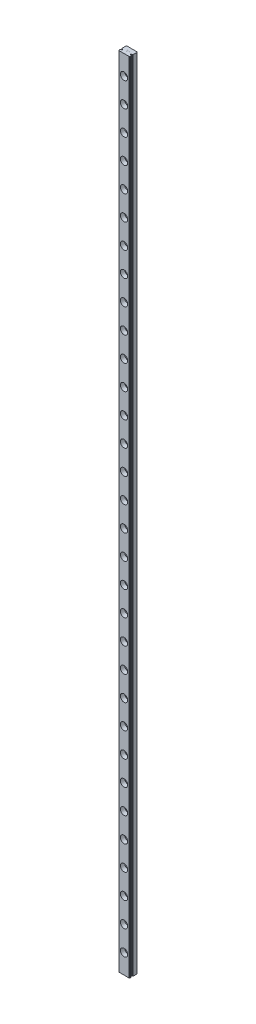
SolidWorks part; units mm, degrees
material "acero"
ref_plane "Alzado" through (0, 0, 0) normal (0, 0, 1) x (1, 0, 0)
ref_plane "Planta" through (0, 0, 0) normal (0, 1, 0) x (1, 0, 0)
ref_plane "Vista lateral" through (0, 0, 0) normal (1, 0, 0) x (0, 0, -1)
ref_plane "Plano1" through (0, 0, 0) normal (0, -1, 0) x (1, 0, 0)
sketch "Croquis1" plane through (0, 0, 0) normal (0, -1, 0) x (1, 0, 0)
  line L0 (4.5, 0) -> (4.5, 6.0117)
  line L1 (4.5, 6.0117) -> (4.1, 6.5)
  line L2 (4.1, 6.5) -> (-4.1, 6.5)
  line L3 (-4.1, 6.5) -> (-4.5, 6.0117)
  line L4 (-4.5, 6.0117) -> (-4.5, 0)
  line L5 (-4.5, 0) -> (4.5, 0)
extrude "Saliente-Extruir1" add sketch "Croquis1" against normal blind 652
sketch "Croquis2" plane through (0, 652, 0) normal (0, 1, 0) x (-1, 0, 0)
  line L0 (-4.5, 4.8802) -> (-4.5, 4.0315)
  line L1 (-4.5, 4.0315) -> (-3.8193, 4.0315)
  line L2 (-3.8193, 4.8802) -> (-4.5, 4.8802)
  arc A1 (-3.8193, 4.0315) -> (-3.8193, 4.8802) centre (-3.6695, 4.4558) ccw
  dimension "D4" = 0.9
  dimension "D2" = 0.8487
extrude "Cortar-Extruir1" cut sketch "Croquis2" against normal through all
sketch "Croquis3" plane through (0, 652, 0) normal (0, 1, 0) x (-1, 0, 0)
  line L0 (-4.0265, 4.0315) -> (-4.5, 4.0315)
  line L1 (-4.5, 4.0315) -> (-4.5, 3.5836)
  arc A0 (-4.5, 3.5836) -> (-4.0265, 4.0315) centre (-4.8765, 4.4558) ccw
extrude "Cortar-Extruir2" cut sketch "Croquis3" against normal through all
sketch "Croquis4" plane through (0, 652, 0) normal (0, 1, 0) x (-1, 0, 0)
  line L0 (-4.5, 5.3281) -> (-4.5, 4.8802)
  line L1 (-4.5, 4.8802) -> (-4.0265, 4.8802)
  arc A0 (-4.0265, 4.8802) -> (-4.5, 5.3281) centre (-4.8765, 4.4558) ccw
extrude "Cortar-Extruir3" cut sketch "Croquis4" against normal through all
sketch "Croquis5" plane through (0, 652, 0) normal (0, 1, 0) x (-1, 0, 0)
  line L0 (4.5, 4.0315) -> (4.5, 4.8802)
  line L1 (4.5, 4.8802) -> (3.8193, 4.8802)
  line L2 (3.8193, 4.0315) -> (4.5, 4.0315)
  arc A1 (3.8193, 4.8802) -> (3.8193, 4.0315) centre (3.6695, 4.4558) ccw
  dimension "D3" = 0.9
  dimension "D2" = 0.8487
extrude "Cortar-Extruir4" cut sketch "Croquis5" against normal through all
sketch "Croquis6" plane through (0, 652, 0) normal (0, 1, 0) x (-1, 0, 0)
  line L0 (4.0265, 4.8802) -> (4.5, 4.8802)
  line L1 (4.5, 4.8802) -> (4.5, 5.3281)
  arc A0 (4.5, 5.3281) -> (4.0265, 4.8802) centre (4.8765, 4.4558) ccw
extrude "Cortar-Extruir5" cut sketch "Croquis6" against normal through all
sketch "Croquis7" plane through (0, 652, 0) normal (0, 1, 0) x (-1, 0, 0)
  line L0 (4.5, 3.5836) -> (4.5, 4.0315)
  line L1 (4.5, 4.0315) -> (4.0265, 4.0315)
  arc A0 (4.0265, 4.0315) -> (4.5, 3.5836) centre (4.8765, 4.4558) ccw
extrude "Cortar-Extruir6" cut sketch "Croquis7" against normal through all
sketch "Croquis8" plane through (0, 652, 0) normal (0, 1, 0) x (-1, 0, 0)
  line L0 (0.8914, 3.4037) -> (0.7147, 3.1682)
  line L1 (0.7147, 3.1682) -> (0.2187, 2.611)
  line L2 (0.2187, 2.611) -> (1.0946, 2.6111)
  line L3 (1.0946, 2.6111) -> (1.0946, 2.696)
  line L4 (1.0946, 2.696) -> (0.3987, 2.696)
  line L5 (0.3987, 2.696) -> (0.7943, 3.1495)
  line L6 (0.7943, 3.1495) -> (0.9743, 3.3891)
  line L7 (0.9743, 3.3891) -> (1.0671, 3.5734)
  line L8 (1.0671, 3.5734) -> (0.9541, 3.8023)
  line L9 (0.9541, 3.8023) -> (0.7877, 3.8851)
  line L10 (0.7877, 3.8851) -> (0.543, 3.8851)
  line L11 (0.543, 3.8851) -> (0.3754, 3.8036)
  line L12 (0.3754, 3.8036) -> (0.295, 3.6384)
  line L13 (0.295, 3.6384) -> (0.295, 3.562)
  line L14 (0.295, 3.562) -> (0.3813, 3.562)
  line L15 (0.3813, 3.562) -> (0.3813, 3.6318)
  line L16 (0.3813, 3.6318) -> (0.4377, 3.7436)
  line L17 (0.4377, 3.7436) -> (0.5496, 3.8001)
  line L18 (0.5496, 3.8001) -> (0.7802, 3.8001)
  line L19 (0.7802, 3.8001) -> (0.893, 3.7438)
  line L20 (0.893, 3.7438) -> (0.9762, 3.576)
  line L21 (0.9762, 3.576) -> (0.8914, 3.4037)
extrude "Cortar-Extruir7" cut sketch "Croquis8" against normal blind 0.0022
sketch "Croquis9" plane through (0, 0, 0) normal (0, -1, 0) x (1, 0, 0)
  line L0 (-0.2146, 3.8851) -> (-0.954, 3.8851)
  line L1 (-0.954, 3.8851) -> (-0.954, 2.6111)
  line L2 (-0.954, 2.6111) -> (-0.2146, 2.6111)
  line L3 (-0.2146, 2.6111) -> (-0.2146, 2.696)
  line L4 (-0.2146, 2.696) -> (-0.869, 2.696)
  line L5 (-0.869, 2.696) -> (-0.869, 3.2056)
  line L6 (-0.869, 3.2056) -> (-0.5124, 3.2056)
  line L7 (-0.5124, 3.2056) -> (-0.5124, 3.2905)
  line L8 (-0.5124, 3.2905) -> (-0.869, 3.2905)
  line L9 (-0.869, 3.2905) -> (-0.869, 3.8001)
  line L10 (-0.869, 3.8001) -> (-0.2146, 3.8001)
  line L11 (-0.2146, 3.8001) -> (-0.2146, 3.8851)
extrude "Cortar-Extruir8" cut sketch "Croquis9" against normal blind 0.0022
sketch "Croquis10" plane through (0, 652, 0) normal (0, 1, 0) x (-1, 0, 0)
  line L0 (-0.2146, 3.8851) -> (-0.954, 3.8851)
  line L1 (-0.954, 3.8851) -> (-0.954, 2.6111)
  line L2 (-0.954, 2.6111) -> (-0.2146, 2.6111)
  line L3 (-0.2146, 2.6111) -> (-0.2146, 2.696)
  line L4 (-0.2146, 2.696) -> (-0.869, 2.696)
  line L5 (-0.869, 2.696) -> (-0.869, 3.2056)
  line L6 (-0.869, 3.2056) -> (-0.5124, 3.2056)
  line L7 (-0.5124, 3.2056) -> (-0.5124, 3.2905)
  line L8 (-0.5124, 3.2905) -> (-0.869, 3.2905)
  line L9 (-0.869, 3.2905) -> (-0.869, 3.8001)
  line L10 (-0.869, 3.8001) -> (-0.2146, 3.8001)
  line L11 (-0.2146, 3.8001) -> (-0.2146, 3.8851)
extrude "Cortar-Extruir9" cut sketch "Croquis10" against normal blind 0.0022
sketch "Croquis11" plane through (0, 0, 0) normal (0, -1, 0) x (1, 0, 0)
  line L0 (0.5101, 3.6208) -> (0.6071, 3.7187)
  line L1 (0.6071, 3.7187) -> (0.6071, 2.6094)
  line L2 (0.6071, 2.6094) -> (0.692, 2.6094)
  line L3 (0.692, 2.6094) -> (0.692, 3.8834)
  line L4 (0.692, 3.8834) -> (0.6741, 3.8834)
  line L5 (0.6741, 3.8834) -> (0.6741, 3.7951)
  line L6 (0.6741, 3.7951) -> (0.3691, 3.6407)
  line L7 (0.3691, 3.6407) -> (0.3691, 3.5513)
  line L8 (0.3691, 3.5513) -> (0.5101, 3.6208)
extrude "Cortar-Extruir10" cut sketch "Croquis11" against normal blind 0.0022
draft "Ángulo de salida1" type of draft neutral plane draft angle 45.147 faces to draft 1 face at (0.6741, 0.0011, 3.8392) neutral plane through (0.692, 0.0022, 3.8834) neutral plane normal (0, 0, -1) parameters "D1"=45.147
chamfer "Chaflán1" distance 0.4 angle 45 2 edges at (4.5, 326, 0) (-4.5, 326, 0)
fillet "Redondeo1" radius 0.13 8 edges at (4.5, 326, 3.5836) (4.0265, 326, 4.0315) (-4.0265, 326, 4.0315) (-4.0265, 326, 4.8802) (-4.5, 326, 5.3281) (-4.5, 326, 3.5836) (4.5, 326, 5.3281) (4.0265, 326, 4.8802)
hole_wizard "Taladro roscado M3.5x0.61" positions "Croquis35" profile "Croquis34" tap size "M3.5x0.6" standard "Ansi Metric"
sketch "Croquis35" plane through (0, 0, 0) normal (0, 0, -1) x (-1, 0, 0)
  line L3 (0, -8.7858) -> (0, 652) construction
  line L5 (-4.1, 652) -> (4.1, 652) construction
  line L6 (-4.1, 0) -> (4.1, 0) construction
  point P39 (0, 16)
sketch "Croquis34" plane through (0, 16, 0) normal (1, 0, 0) x (0, 1, 0)
  line L0 (0, 0) -> (0, 8)
  line L1 (0, 8) -> (3, 8)
  line L2 (3, 8) -> (3, 3)
  line L3 (3, 3) -> (1.75, 3)
  line L4 (1.75, 3) -> (1.75, 0)
  line L5 (1.75, 0) -> (0, 0)
  line L10 (0, 8) -> (-3, 8) construction
  line L11 (0, -6.35) -> (0, 107.95) construction
  dimension "Diámetro de perforador para roscar" = 6
  dimension "Profundidad de perforador para roscar" = 8
  dimension "Diámetro mayor de rosca" = 3.5
  dimension "Profundidad de rosca" = 3
  dimension "Ángulo de perforador" = 180
sketch "Croquis37" plane through (0, 0, 6.5) normal (0, 0, 1) x (1, 0, 0)
  line L0 (0, -8.7858) -> (0, 652) construction
  line L1 (0, -8.7858) -> (0, 652) construction
  line L2 (4.1, 652) -> (-4.1, 652) construction
  point P2 (0, 636)
pattern_linear "MatrizL2" count 32 spacing 20 along (0, 1, 0) of "Taladro roscado M3.5x0.61"
